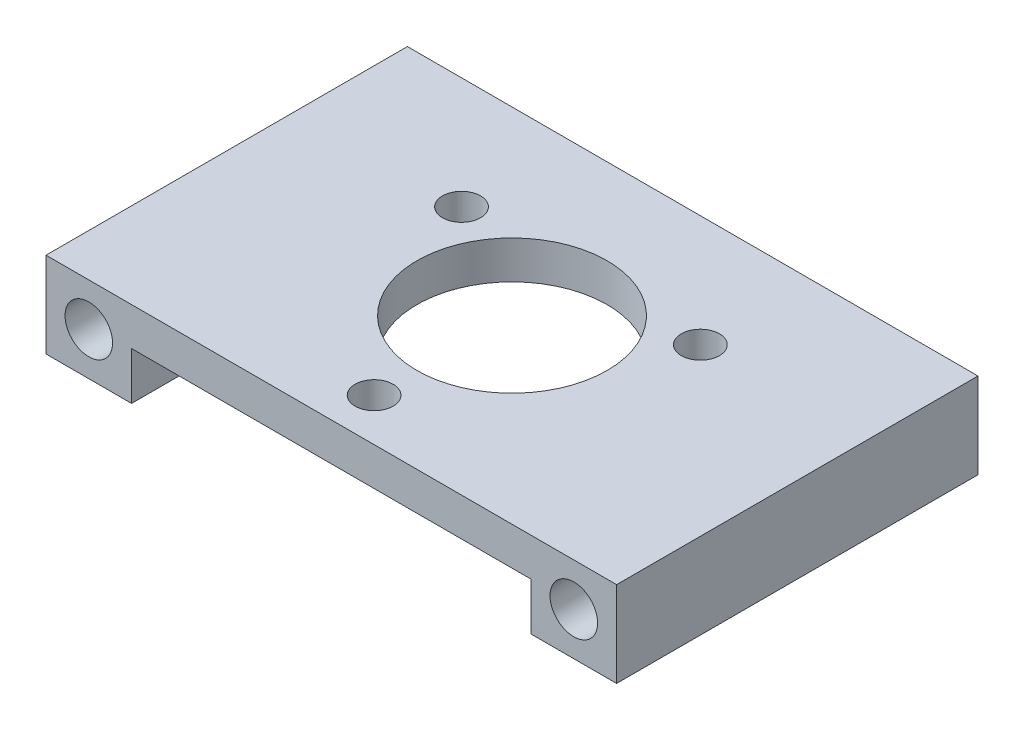
SolidWorks part; units mm, degrees
ref_plane "Front Plane" through (0, 0, 0) normal (0, 0, 1) x (1, 0, 0)
ref_plane "Top Plane" through (0, 0, 0) normal (0, 1, 0) x (1, 0, 0)
ref_plane "Right Plane" through (0, 0, 0) normal (1, 0, 0) x (0, 0, -1)
sketch "Sketch1" plane through (0, 0, 0) normal (0, 0, 1) x (1, 0, 0)
  line L0 (-30, 0) -> (-30, -9)
  line L1 (-30, -9) -> (-21, -9)
  line L2 (-21, -9) -> (-21, -4)
  line L3 (-21, -4) -> (21, -4)
  line L8 (-30, 0) -> (30, 0)
  line L11 (21, -9) -> (21, -4)
  line L12 (30, -9) -> (21, -9)
  line L13 (30, 0) -> (30, -9)
  circle A0 centre (-25.5, -4.5) radius 2.5
  circle A4 centre (25.5, -4.5) radius 2.5
  dimension "D10" = 5
  dimension "D3" = 4.5
  dimension "D9" = 5
  dimension "D1" = 9
  dimension "D2" = 9
  dimension "D4" = 4
  dimension "D5" = 60
  dimension "D6" = 9
  dimension "D7" = 4.5
  dimension "D8" = 9
  dimension "D11" = 51
  dimension "D12" = 21
extrude "Boss-Extrude1" add sketch "Sketch1" along normal blind 38
sketch "Sketch2" plane through (0, -4, 0) normal (0, -1, 0) x (1, 0, 0)
  line L0 (-30, 38) -> (-30, 0) construction
  line L2 (-21, 0) -> (21, 0) construction
  circle A0 centre (0, 19) radius 10
  circle A1 centre (0, 33.5) radius 2
  circle A8 centre (12.5574, 11.75) radius 2
  circle A9 centre (-12.5574, 11.75) radius 2
  point P15 (0, 19)
  point P17 (0, 19)
  dimension "D3" = 20
  dimension "D4" = 4
  dimension "D1" = 30
  dimension "D2" = 19
  dimension "D5" = 14.5
  dimension "D6" = 3
extrude "Cut-Extrude1" cut sketch "Sketch2" against normal blind 38
